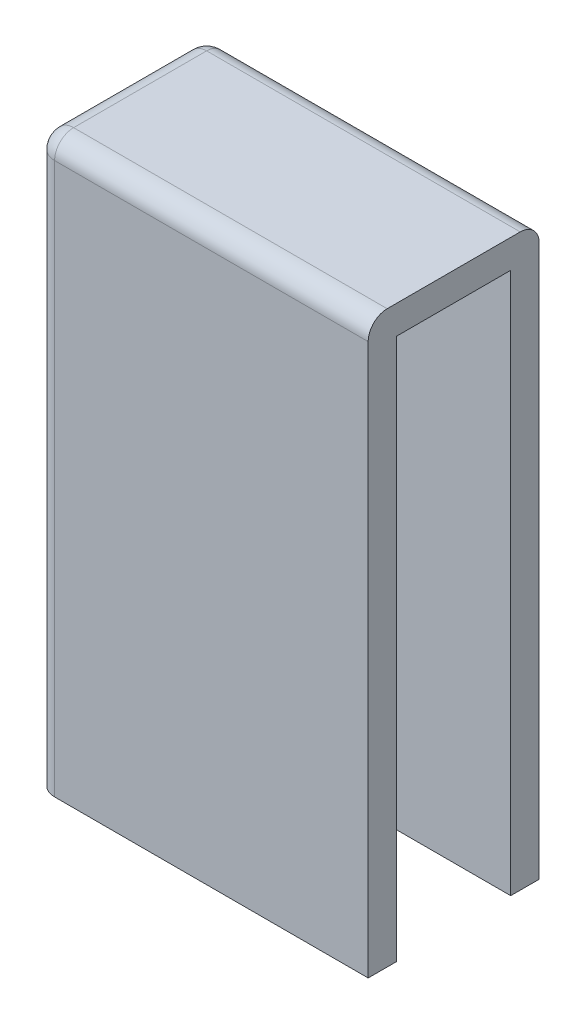
SolidWorks part; units mm, degrees
ref_plane "Front Plane" through (0, 0, 0) normal (0, 0, 1) x (1, 0, 0)
ref_plane "Top Plane" through (0, 0, 0) normal (0, 1, 0) x (1, 0, 0)
ref_plane "Right Plane" through (0, 0, 0) normal (1, 0, 0) x (0, 0, -1)
sketch "Sketch1" plane through (0, 0, 0) normal (0, 1, 0) x (1, 0, 0)
  line L0 (0, 0) -> (-32, 0)
  line L1 (-32, 0) -> (-32, 12)
  line L2 (-32, 12) -> (0, 12)
  line L3 (0, -3) -> (-35, -3)
  line L4 (-35, -3) -> (-35, 15)
  line L5 (-35, 15) -> (0, 15)
  line L6 (0, 12) -> (0, 15)
  line L7 (0, 0) -> (0, -3)
  dimension "D1" = 32
  dimension "D2" = 12
  dimension "D3" = 3
extrude "Boss-Extrude1" add sketch "Sketch1" along normal blind 57
sketch "Sketch2" plane through (0, 57, 0) normal (0, 1, 0) x (1, 0, 0)
  line L1 (-35, 15) -> (0, 15)
  line L2 (-35, 15) -> (-35, -3)
  line L3 (-35, -3) -> (0, -3)
  line L4 (0, 15) -> (0, -3)
extrude "Boss-Extrude2" add sketch "Sketch2" along normal blind 3
fillet "Fillet1" radius 2 5 edges at (-17.5, 60, -15) (-35, 30, -15) (-35, 30, 3) (-35, 60, -6) (-17.5, 60, 3)
